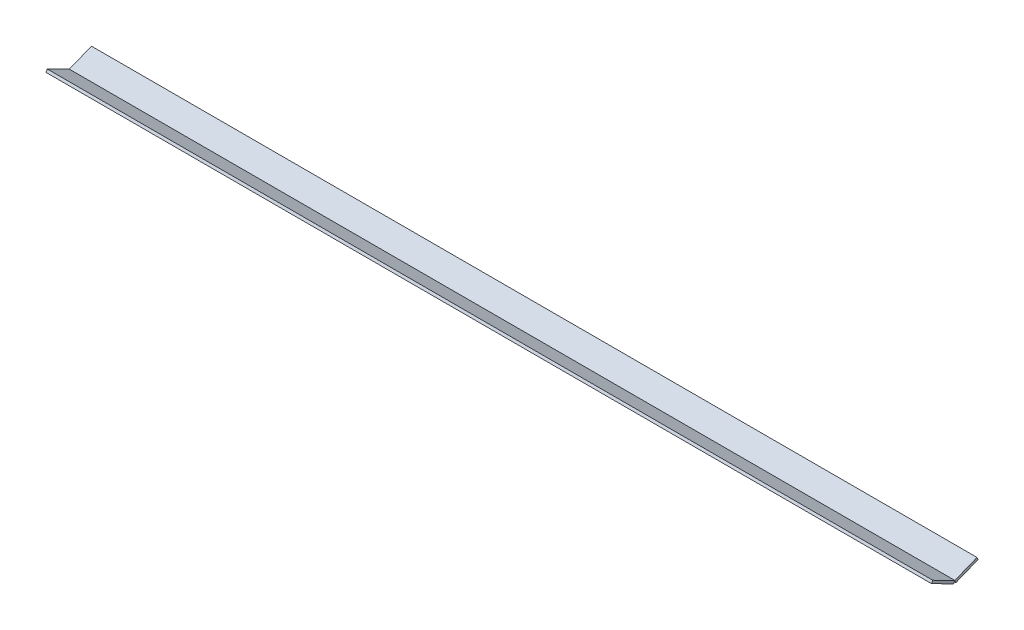
SolidWorks part; units mm, degrees
ref_plane "Front Plane" through (0, 0, 0) normal (0, 0, 1) x (1, 0, 0)
ref_plane "Top Plane" through (0, 0, 0) normal (0, 1, 0) x (1, 0, 0)
ref_plane "Right Plane" through (0, 0, 0) normal (1, 0, 0) x (0, 0, -1)
sketch "Sketch2" plane through (0, 0, 0) normal (1, 0, 0) x (0, 0, -1)
  line L0 (-26.3567, 10) -> (-25, 12.6757)
  line L1 (-25, 12.6757) -> (0, 0)
  line L2 (0, 0) -> (-1.3567, -2.6757)
  line L3 (-1.3567, -2.6757) -> (-26.3567, 10)
  line L4 (26.1142, 7.2146) -> (1.1142, -2.7854)
  line L5 (1.1142, -2.7854) -> (0, 0)
  line L6 (0, 0) -> (25, 10)
  line L7 (25, 10) -> (26.1142, 7.2146)
  point P0 (1.3703, -3.4257)
  point P2 (-118.9875, 50.2628)
  dimension "D1" = 10
  dimension "D2" = 3
  dimension "D3" = 25
  dimension "D4" = 25
  dimension "D5" = 10
  dimension "D6" = 3
extrude "Boss-Extrude1" add sketch "Sketch2" along normal blind 1000 contours L3 L2 L1 L0 | L7 L6 L5 L4
